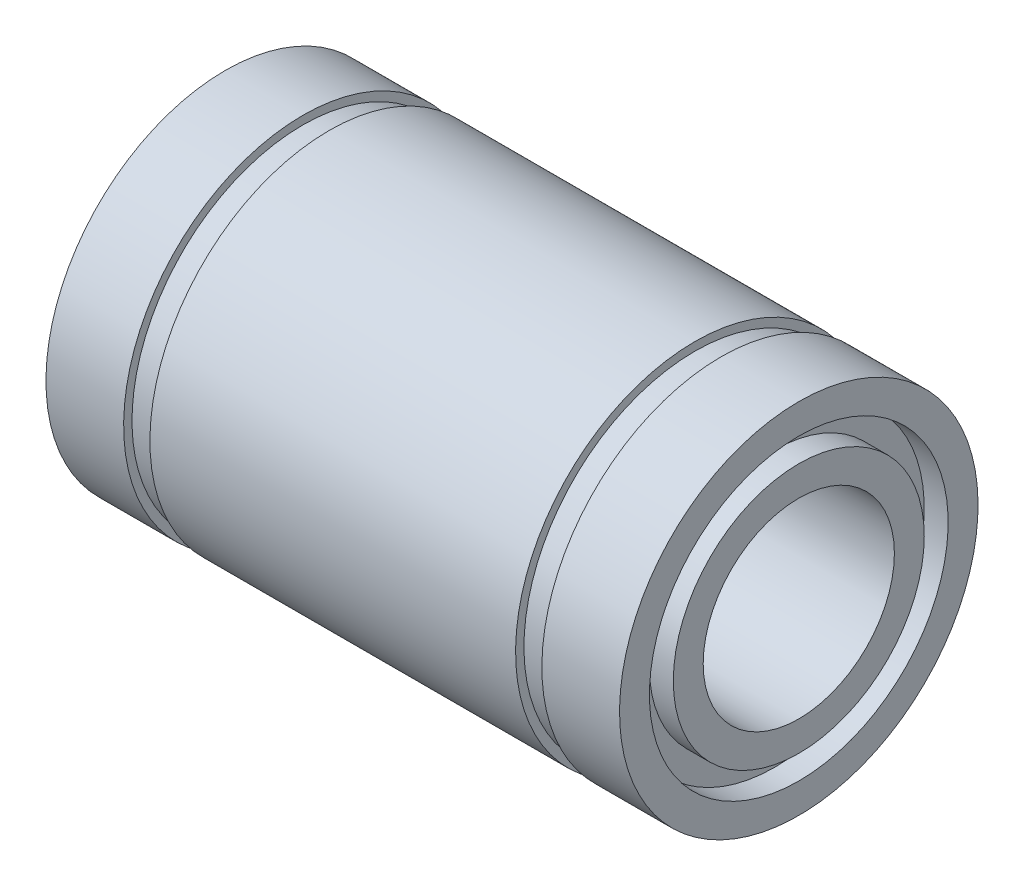
SolidWorks part; units mm, degrees
material "Ст3сп ГОСТ 535-2005"
ref_plane "Plano frontal" through (0, 0, 0) normal (0, 0, 1) x (1, 0, 0)
ref_plane "Plano superior" through (0, 0, 0) normal (0, 1, 0) x (1, 0, 0)
ref_plane "Plano direito" through (0, 0, 0) normal (1, 0, 0) x (0, 0, -1)
sketch "Esboço1" plane through (0, 0, 0) normal (0, 0, 1) x (1, 0, 0)
  line L0 (-12, 7.5) -> (-8.75, 7.5)
  line L1 (-8.75, 7.5) -> (-8.75, 7.15)
  line L2 (-8.75, 7.15) -> (-7.65, 7.15)
  line L3 (-7.65, 7.15) -> (-7.65, 7.5)
  line L4 (-7.65, 7.5) -> (7.65, 7.5)
  line L5 (7.65, 7.5) -> (7.65, 7.15)
  line L6 (7.65, 7.15) -> (8.75, 7.15)
  line L7 (8.75, 7.15) -> (8.75, 7.5)
  line L8 (8.75, 7.5) -> (12, 7.5)
  line L9 (12, 7.5) -> (12, 6.25)
  line L10 (12, 4) -> (-12, 4)
  line L11 (-12, 4) -> (-12, 5.25)
  line L12 (0, 4) -> (0, 0) construction
  line L13 (0, 0) -> (-86.5, 0) construction
  line L14 (-12, 6.25) -> (-12, 7.5)
  line L15 (-12, 6.25) -> (-11, 6.25)
  line L16 (12, 5.25) -> (12, 4)
  line L17 (-11, 6.25) -> (-11, 5.25)
  line L18 (-11, 5.25) -> (-12, 5.25)
  line L19 (12, 6.25) -> (11, 6.25)
  line L21 (12, 5.25) -> (11, 5.25)
  line L22 (11, 6.25) -> (11, 5.25)
  dimension "D1" = 24
  dimension "D2" = 17.5
  dimension "D3" = 1.1
  dimension "D4" = 8
  dimension "D5" = 15
  dimension "D6" = 14.3
  dimension "D7" = 1
  dimension "D8" = 1
  dimension "D9" = 1
  dimension "D10" = 1
revolve "Revolução1" add sketch "Esboço1" angle 360 about L13
